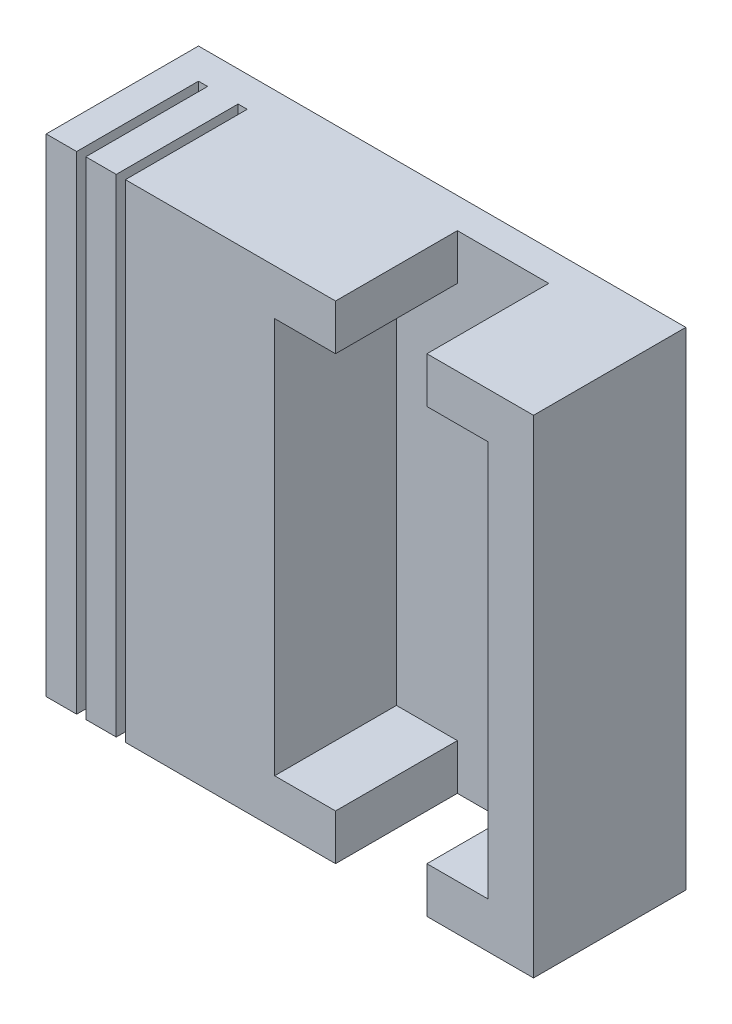
SolidWorks part; units mm, degrees
ref_plane "Front Plane" through (0, 0, 0) normal (1, 0, 0) x (0, 1, 0)
ref_plane "Top Plane" through (0, 0, 0) normal (0, 0, 1) x (0, 1, 0)
ref_plane "Right Plane" through (0, 0, 0) normal (0, 1, 0) x (-1, 0, 0)
sketch "Sketch1" plane through (0, 0, 0) normal (0, 0, 1) x (0, 1, 0)
  line L1 (0, 0) -> (20.32, 0)
  line L2 (0, 0) -> (0, 20.32)
  line L3 (0, 20.32) -> (20.32, 20.32)
  line L4 (20.32, 0) -> (20.32, 20.32)
  dimension "D1" = 20.32
  dimension "D2" = 20.32
extrude "Boss-Extrude1" add sketch "Sketch1" along normal blind 6.35
sketch "Sketch2" plane through (0, 0, 6.35) normal (0, 0, 1) x (1, 0, 0)
  line L0 (0, 0) -> (0, 20.32) construction
  line L1 (-10.795, 18.415) -> (-8.255, 18.415)
  line L2 (-10.795, 18.415) -> (-10.795, 1.905)
  line L3 (-10.795, 1.905) -> (-8.255, 1.905)
  line L4 (-1.905, 18.415) -> (-1.905, 1.905)
  line L5 (0, 20.32) -> (-20.32, 20.32) construction
  line L6 (-20.32, 0) -> (0, 0) construction
  line L7 (-4.445, 18.415) -> (-1.905, 18.415)
  line L9 (-8.255, 18.415) -> (-8.255, 20.32)
  line L10 (-8.255, 20.32) -> (-4.445, 20.32)
  line L11 (-4.445, 18.415) -> (-4.445, 20.32)
  line L13 (-8.255, 1.905) -> (-8.255, -0.5329)
  line L14 (-8.255, -0.5329) -> (-4.445, -0.5329)
  line L15 (-4.445, 1.905) -> (-4.445, -0.5329)
  line L16 (-4.445, 1.905) -> (-1.905, 1.905)
  dimension "D1" = 1.905
  dimension "D2" = 1.905
  dimension "D3" = 1.905
  dimension "D4" = 3.81
  dimension "D5" = 3.81
  dimension "D7" = 8.89
extrude "Cut-Extrude1" cut sketch "Sketch2" against normal blind 5.08
sketch "Sketch4" plane through (0, 0, 6.35) normal (0, 0, 1) x (1, 0, 0)
  line L0 (-20.32, 20.32) -> (-20.32, 0) construction
  line L1 (-19.05, 20.7812) -> (-18.669, 20.7812)
  line L2 (-19.05, 20.7812) -> (-19.05, -0.8674)
  line L3 (-19.05, -0.8674) -> (-18.669, -0.8674)
  line L4 (-18.669, 20.7812) -> (-18.669, -0.8674)
  line L5 (-17.399, 20.7812) -> (-17.018, 20.7812)
  line L6 (-17.399, 20.7812) -> (-17.399, -0.8674)
  line L7 (-17.399, -0.8674) -> (-17.018, -0.8674)
  line L8 (-17.018, 20.7812) -> (-17.018, -0.8674)
  dimension "D1" = 1.27
  dimension "D2" = 1.27
  dimension "D3" = 0.381
  dimension "D4" = 0.381
extrude "Cut-Extrude2" cut sketch "Sketch4" against normal blind 5.08
